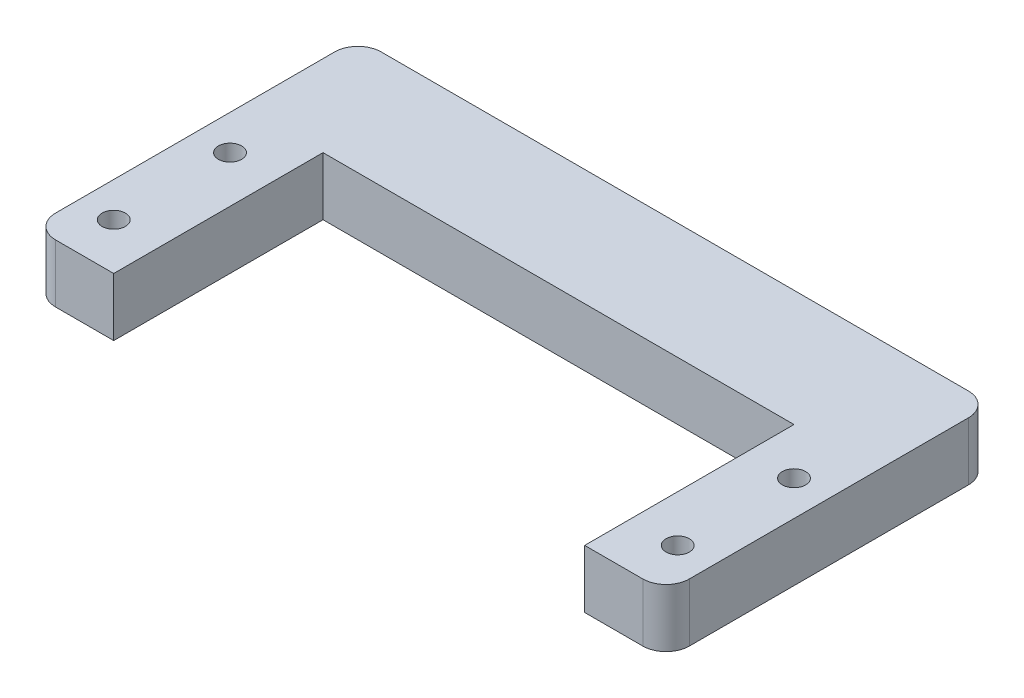
SolidWorks part; units mm, degrees
ref_plane "Alzado" through (0, 0, 0) normal (0, 0, 1) x (1, 0, 0)
ref_plane "Planta" through (0, 0, 0) normal (0, 1, 0) x (1, 0, 0)
ref_plane "Vista lateral" through (0, 0, 0) normal (1, 0, 0) x (0, 0, -1)
sketch "Sketch1" plane through (0, 0, 0) normal (0, 1, 0) x (1, 0, 0)
  line L0 (-24.25, 0) -> (24.25, 0) construction
  line L1 (24.25, 5) -> (24.25, -5) construction
  line L2 (-24.25, 5) -> (-24.25, -5) construction
  line L3 (-24.25, -9) -> (-20.25, -9) construction
  line L4 (-24.25, -9) -> (-27.25, -9) construction
  line L5 (-24.25, -5) -> (-24.25, -9) construction
  line L6 (-24.25, 5) -> (-24.25, 9) construction
  line L7 (0, -15.5836) -> (0, 15.5836) construction
  line L8 (-20.25, -9) -> (-25.25, -9)
  line L9 (-20.25, -9) -> (-20.25, 9)
  line L10 (-20.25, 9) -> (-27.25, 9)
  line L11 (-27.25, -7) -> (-27.25, 9)
  line L12 (20.25, 9) -> (27.25, 9)
  line L13 (27.25, -7) -> (27.25, 9)
  line L14 (20.25, -9) -> (25.25, -9)
  line L15 (20.25, -9) -> (20.25, 9)
  line L17 (27.25, 9) -> (-27.25, 9)
  line L18 (27.25, 9) -> (27.25, 19)
  line L19 (27.25, 19) -> (-27.25, 19)
  line L20 (-27.25, 9) -> (-27.25, 19)
  circle A0 centre (-24.25, -5) radius 1
  circle A1 centre (24.25, -5) radius 1
  circle A2 centre (24.25, 5) radius 1
  circle A3 centre (-24.25, 5) radius 1
  arc A4 (27.25, -7) -> (25.25, -9) centre (25.25, -7) cw
  arc A5 (-25.25, -9) -> (-27.25, -7) centre (-25.25, -7) cw
  point P3 (0, 0)
  point P6 (24.25, 0)
  point P11 (-24.25, 0)
  point P26 (0, 0)
  point P32 (27.25, -9)
  point P35 (-27.25, -9)
  dimension "D4" = 2
  dimension "D7" = 4
  dimension "D11" = 2
  dimension "D1" = 48.5
  dimension "D2" = 5
  dimension "D3" = 5
  dimension "D8" = 3
  dimension "D9" = 4
  dimension "D10" = 4
  dimension "D12" = 10
  dimension "D5" = 2
  dimension "D6" = 2
extrude "Boss-Extrude2" add sketch "Sketch1" along normal blind 5 contours A5 L8 L9 L10 L11 A0 A3 | L20 L10 L17 L12 L18 L19 | A4 L13 L12 L15 L14 A2 A1
fillet "Fillet1" radius 2 2 edges at (27.25, 2.5, -19) (-27.25, 2.5, -19)
